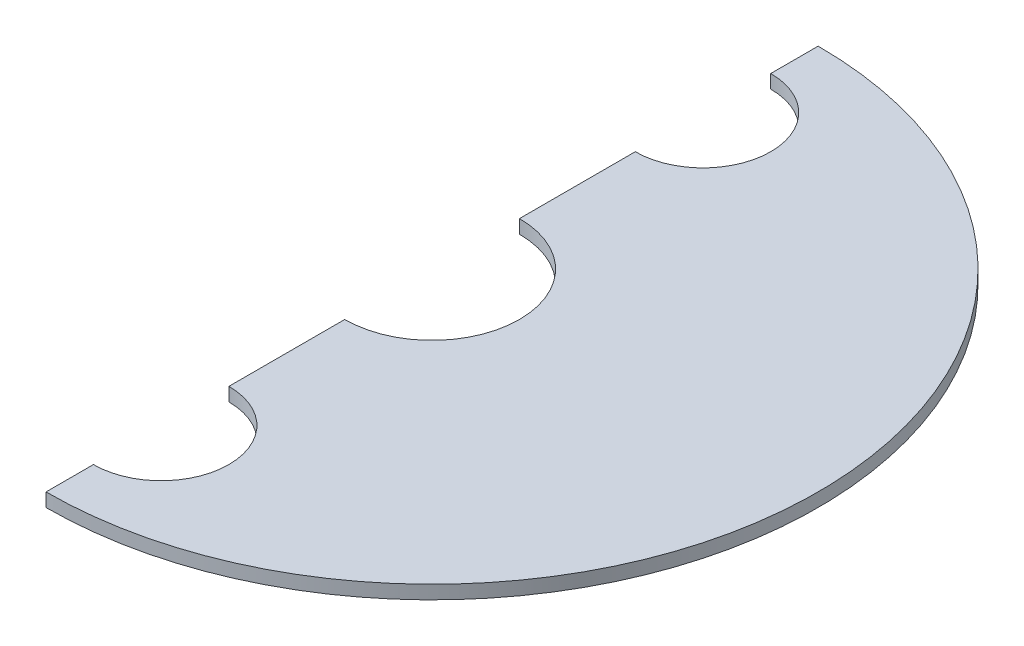
SolidWorks part; units mm, degrees
ref_plane "Front Plane" through (0, 0, 0) normal (0, 0, 1) x (1, 0, 0)
ref_plane "Top Plane" through (0, 0, 0) normal (0, 1, 0) x (1, 0, 0)
ref_plane "Right Plane" through (0, 0, 0) normal (1, 0, 0) x (0, 0, -1)
sketch "Sketch1" plane through (0, 0, 0) normal (0, 1, 0) x (1, 0, 0)
  line L0 (0, 6.45) -> (0, 15)
  line L1 (0, 28.5) -> (0, 25)
  line L2 (0, -6.45) -> (0, -15)
  line L3 (0, -25) -> (0, -28.5)
  line L4 (0, 25) -> (0, 28.5)
  line L5 (0, 15) -> (0, 6.45)
  arc A0 (0, -28.5) -> (0, 28.5) centre (0, 0) ccw
  arc A1 (0, -6.45) -> (0, 6.45) centre (0, 0) ccw
  arc A2 (0, -25) -> (0, -15) centre (0, -20) ccw
  arc A3 (0, 15) -> (0, 25) centre (0, 20) ccw
  dimension "D1" = 57
  dimension "D2" = 12.9
  dimension "D3" = 10
  dimension "D5" = 10
  dimension "D4" = 20
  dimension "D6" = 20
extrude "Boss-Extrude1" add sketch "Sketch1" along normal blind 1 contours A1 L2 A0 L0
